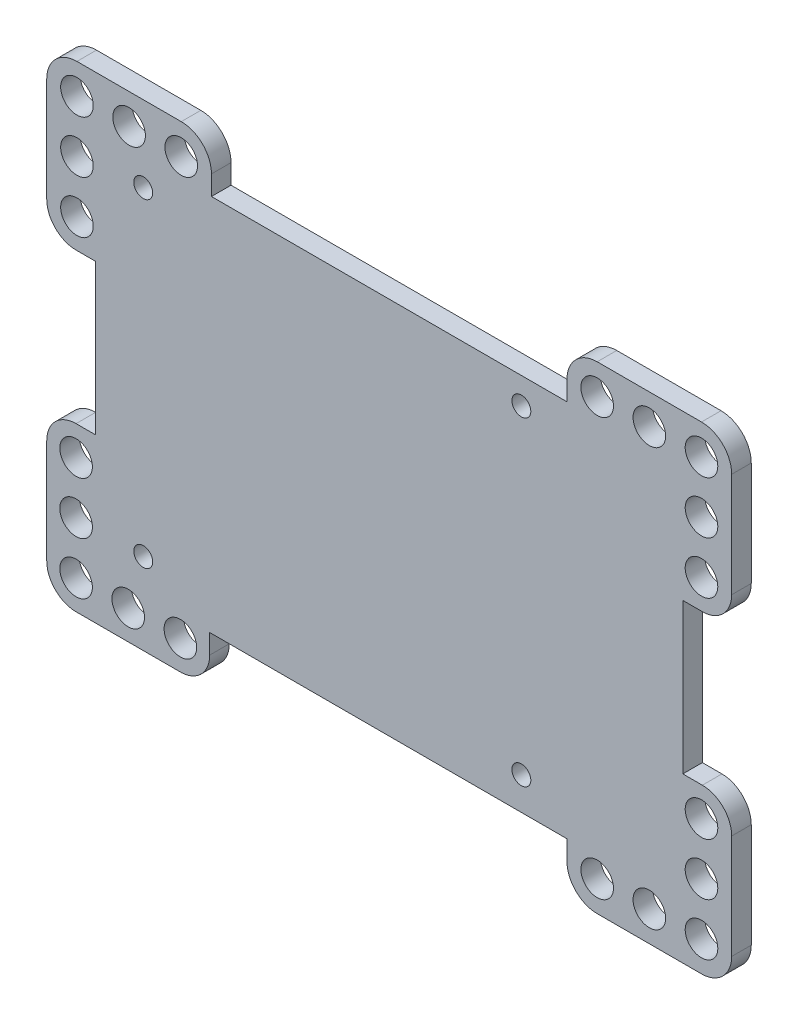
SolidWorks part; units mm, degrees
ref_plane "前基準面" through (0, 0, 0) normal (0, 0, 1) x (1, 0, 0)
ref_plane "上基準面" through (0, 0, 0) normal (0, 1, 0) x (1, 0, 0)
ref_plane "右基準面" through (0, 0, 0) normal (1, 0, 0) x (0, 0, -1)
sketch "草圖1" plane through (0, 0, 0) normal (0, 0, 1) x (1, 0, 0)
  line L0 (28.2337, 33.4111) -> (28.2337, -30.6389) construction
  line L1 (28.2337, -30.6389) -> (-35.6987, -30.6389) construction
  line L2 (-51.6987, 12.9111) -> (-48.6987, 12.9111)
  line L3 (-56.1987, 33.4111) -> (-56.1987, 17.4111)
  line L4 (-51.5663, 38.0435) -> (-35.5663, 38.0435)
  line L5 (-30.934, 33.4111) -> (-30.934, 30.4111)
  line L6 (44.366, 12.9111) -> (41.366, 12.9111)
  line L7 (48.866, 33.4111) -> (48.866, 17.4111)
  line L16 (-51.6987, -10.1389) -> (-48.6987, -10.1389)
  line L17 (-56.1987, -30.6389) -> (-56.1987, -14.6389)
  line L18 (-51.5663, -35.1369) -> (-35.5663, -35.1369)
  line L19 (-31.1987, -30.6389) -> (-31.1987, -27.6389)
  line L20 (-30.934, 30.4111) -> (23.7337, 30.4111)
  line L21 (-48.6987, 12.9111) -> (-48.6987, -10.1389)
  line L22 (-31.1987, -27.6389) -> (23.6013, -27.6389)
  line L24 (-51.5663, 33.4111) -> (-51.5663, -38.0429) construction
  line L25 (-35.6987, -30.6389) -> (-51.6987, -30.6389) construction
  line L26 (-48.6987, 1.3861) -> (28.2337, 1.3861) construction
  line L27 (-35.5663, 33.4111) -> (28.2337, 33.4111) construction
  line L28 (-3.6663, 33.4111) -> (-3.6663, 17.4111) construction
  line L29 (23.6013, 33.4111) -> (23.6013, 30.4111)
  line L30 (44.2337, 38.0435) -> (28.2337, 38.0435)
  line L31 (23.6013, -30.6389) -> (23.6013, -27.6389)
  line L32 (44.2337, -35.2712) -> (28.2337, -35.2712)
  line L33 (48.866, -30.6389) -> (48.866, -14.6389)
  line L34 (44.366, -10.1389) -> (41.366, -10.1389)
  line L35 (41.366, 12.9111) -> (41.366, -10.1389)
  arc A0 (-56.1987, 17.4111) -> (-51.6987, 12.9111) centre (-51.6987, 17.4111) ccw
  arc A1 (-51.5663, 38.0435) -> (-56.1987, 33.4111) centre (-51.5663, 33.4111) ccw
  circle A11 centre (-35.6987, -30.6389) radius 2.5
  arc A16 (-56.1987, -14.6389) -> (-51.6987, -10.1389) centre (-51.6987, -14.6389) cw
  arc A17 (-51.5663, -35.1369) -> (-56.1987, -30.6389) centre (-51.6987, -30.6389) cw
  arc A18 (-35.5663, -35.1369) -> (-31.1987, -30.6389) centre (-35.6987, -30.6389) ccw
  arc A19 (-35.5663, 38.0435) -> (-30.934, 33.4111) centre (-35.5663, 33.4111) cw
  circle A22 centre (-51.5663, 33.4111) radius 2.5
  circle A23 centre (-43.5663, 33.4111) radius 2.5
  circle A24 centre (-35.5663, 33.4111) radius 2.5
  circle A37 centre (-51.5663, 25.4111) radius 2.5
  circle A38 centre (-51.5663, 17.4111) radius 2.5
  circle A39 centre (-43.6987, -30.6389) radius 2.5
  circle A40 centre (-51.6987, -30.6389) radius 2.5
  circle A41 centre (-51.6987, -22.6389) radius 2.5
  circle A42 centre (-51.6987, -14.6389) radius 2.5
  circle A50 centre (-41.3987, 26.3611) radius 1.45
  circle A51 centre (-41.3987, -22.6389) radius 1.45
  circle A52 centre (16.6013, -22.6389) radius 1.45
  circle A53 centre (16.6013, 26.3611) radius 1.45
  circle A54 centre (28.2337, 33.4111) radius 2.5
  circle A55 centre (36.2337, 33.4111) radius 2.5
  circle A61 centre (44.2337, 17.4111) radius 2.5
  circle A62 centre (44.2337, 25.4111) radius 2.5
  circle A63 centre (44.2337, 33.4111) radius 2.5
  arc A64 (48.866, 17.4111) -> (44.366, 12.9111) centre (44.366, 17.4111) cw
  arc A65 (28.2337, 38.0435) -> (23.6013, 33.4111) centre (28.2337, 33.4111) ccw
  arc A66 (44.2337, 38.0435) -> (48.866, 33.4111) centre (44.2337, 33.4111) cw
  arc A67 (28.2337, -35.2712) -> (23.6013, -30.6389) centre (28.2337, -30.6389) cw
  circle A68 centre (28.2337, -30.6389) radius 2.5
  arc A69 (44.2337, -35.2712) -> (48.866, -30.6389) centre (44.2337, -30.6389) ccw
  arc A70 (48.866, -14.6389) -> (44.366, -10.1389) centre (44.366, -14.6389) ccw
  circle A71 centre (44.2337, -30.6389) radius 2.5
  circle A72 centre (44.2337, -22.6389) radius 2.5
  circle A73 centre (44.2337, -14.6389) radius 2.5
  circle A74 centre (36.2337, -30.6389) radius 2.5
  point P20 (23.6013, 31.9111)
  point P25 (23.6013, -29.1389)
  point P47 (-32.2908, 36.6867)
  point P57 (24.9581, 36.6867)
  dimension "D5" = 3
  dimension "D1" = 63.8
  dimension "D2" = 8
  dimension "D4" = 8
  dimension "D8" = 32.05
  dimension "D6" = 3
  dimension "D7" = 3
extrude "填料-伸長2" add sketch "草圖1" along normal blind 3
